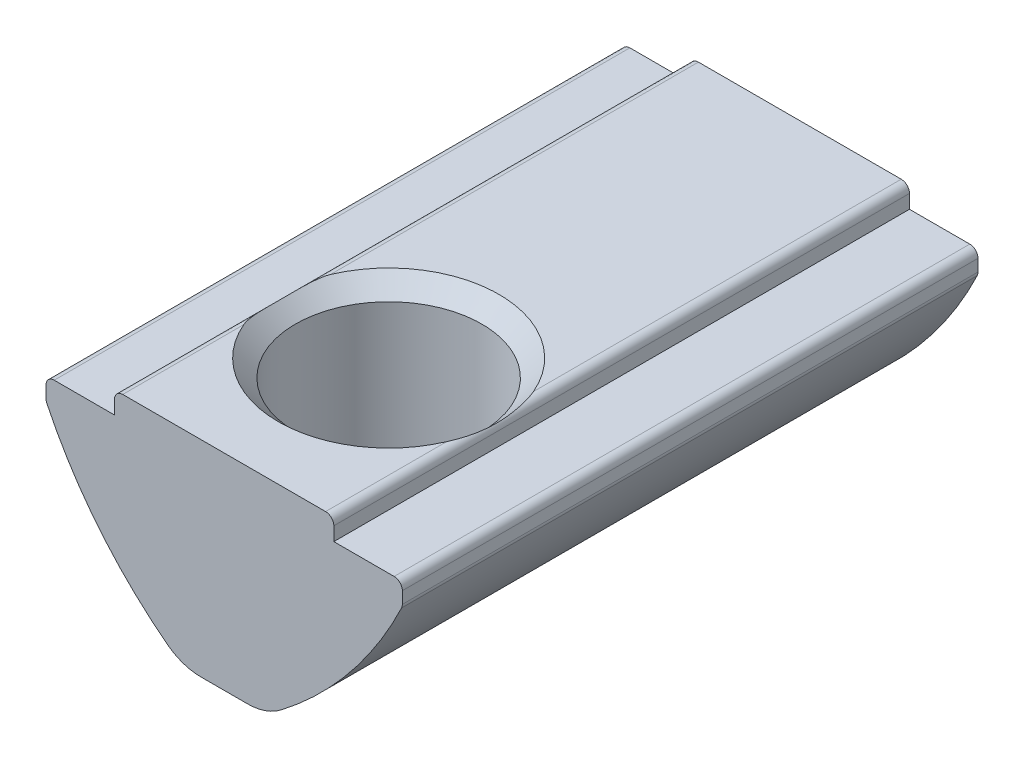
SolidWorks part; units mm, degrees
ref_plane "Спереди" through (0, 0, 0) normal (0, 0, 1) x (1, 0, 0)
ref_plane "Сверху" through (0, 0, 0) normal (0, 1, 0) x (1, 0, 0)
ref_plane "Справа" through (0, 0, 0) normal (1, 0, 0) x (0, 0, -1)
sketch "Эскиз1" plane through (0, 0, 0) normal (0, 0, 1) x (1, 0, 0)
  line L0 (-4, 0) -> (4, 0)
  line L5 (-4, 0) -> (-4, -0.8)
  line L6 (-4, -0.8) -> (-6.5, -0.8)
  line L7 (-6.5, -0.8) -> (-6.5, -1.6)
  line L8 (4, 0) -> (4, -0.8)
  line L9 (4, -0.8) -> (6.5, -0.8)
  line L10 (6.5, -0.8) -> (6.5, -1.6)
  line L11 (-1.5, -7.5) -> (1.5, -7.5)
  arc A0 (-6.5, -1.6) -> (-1.5, -7.5) centre (7.0567, 4.82) ccw
  arc A1 (1.5, -7.5) -> (6.5, -1.6) centre (-7.0567, 4.82) ccw
  point P0 (0, -7.5)
  point P4 (0, 0)
  dimension "D7" = 15
  dimension "D1" = 8
  dimension "D2" = 13
  dimension "D3" = 0.8
  dimension "D4" = 3
  dimension "D5" = 0.8
  dimension "D6" = 7.5
extrude "Бобышка-Вытянуть1" add sketch "Эскиз1" along normal mid plane 21
fillet "Скругление1" radius 0.3 6 edges at (6.5, -1.6, 0) (6.5, -0.8, 0) (-6.5, -0.8, 0) (-6.5, -1.6, 0) (4, 0, 0) (-4, 0, 0)
fillet "Скругление2" radius 2 2 edges at (1.5, -7.5, 0) (-1.5, -7.5, 0)
hole_wizard "Отверстие обработанное метчиком M82" positions "Эскиз2" profile "Эскиз4" tap size "M8" standard "ISO" end condition through all
sketch "Эскиз2" plane through (0, 0, 0) normal (0, 1, 0) x (1, 0, 0)
  line L0 (3.7, -10.5) -> (-3.7, -10.5) construction
  point P0 (0, -4.5)
  dimension "D1" = 6
sketch "Эскиз4" plane through (0, 0, 4.5) normal (1, 0, 0) x (0, 0, 1)
  line L0 (0, 0) -> (0, 7.5)
  line L1 (0, 7.5) -> (3.4, 7.5)
  line L2 (3.4, 7.5) -> (3.4, 0.625)
  line L3 (3.4, 0.625) -> (4.025, 0)
  line L5 (4.025, 0) -> (0, 0)
  line L6 (-3.4, 0.625) -> (-4.025, 0) construction
  line L11 (0, -6.35) -> (0, 107.95) construction
  dimension "Диаметр проходного сверла" = 6.8
  dimension "Глубина проходного сверла" = 7.5
  dimension "Диаметр передней зенковки" = 8.05
  dimension "Угол передней зенковки" = 90
cosmetic thread "Отверстие резьбы1" parameters "D2"=8
sketch "Эскиз5" plane through (0, 0, 0) normal (1, 0, 0) x (0, 0, -1)
  line L1 (6.5, -4.3) -> (6.5, -8.3) construction
  line L2 (10.5, -7.0877) -> (10.5, -1.6618) construction
  line L3 (6.5, -4.3) -> (6.5, -8.3)
  line L5 (10.5, -7.5) -> (-1.2077, -7.5) construction
  arc A0 (6.5, -4.3) -> (6.5, -8.3) centre (6.5, -6.3) ccw
  point P3 (4, -7.4722)
  dimension "D3" = 2
  dimension "D1" = 0.8
  dimension "D2" = 4
revolve "Повернуть1" add sketch "Эскиз5" angle 360 about L1
